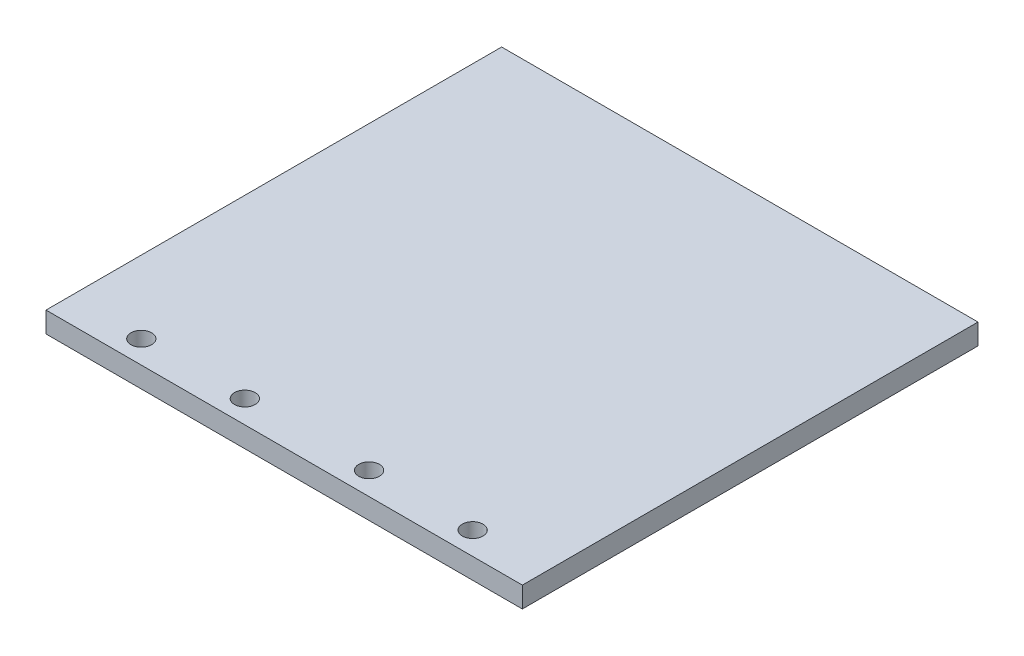
SolidWorks part; units mm, degrees
ref_plane "Front Plane" through (0, 0, 0) normal (0, 0, 1) x (1, 0, 0)
ref_plane "Top Plane" through (0, 0, 0) normal (0, 1, 0) x (1, 0, 0)
ref_plane "Right Plane" through (0, 0, 0) normal (1, 0, 0) x (0, 0, -1)
sketch "Sketch2" plane through (0, 0, 0) normal (0, 1, 0) x (1, 0, 0)
  line L0 (0, 92.2649) -> (0, -97.3417) construction
  line L1 (-57.5, 55) -> (57.5, 55)
  line L2 (-57.5, 55) -> (-57.5, -55)
  line L3 (-57.5, -55) -> (57.5, -55)
  line L4 (57.5, 55) -> (57.5, -55)
  line L5 (-77.6967, 0) -> (99.3282, 0) construction
  dimension "D1" = 115
  dimension "D2" = 110
extrude "Boss-Extrude1" add sketch "Sketch2" along normal blind 5
sketch "Sketch3" plane through (0, 0, 0) normal (0, -1, 0) x (1, 0, 0)
  line L0 (-63.5633, 49.5) -> (69.5866, 49.5) construction
  line L2 (-57.5, 55) -> (57.5, 55) construction
  line L3 (0, 53.104) -> (0, -54.2302) construction
  circle A2 centre (-40, 49.5) radius 2.5
  circle A3 centre (-15, 49.5) radius 2.5
  circle A4 centre (40, 49.5) radius 2.5
  circle A5 centre (15, 49.5) radius 2.5
  dimension "D1" = 5
  dimension "D2" = 5
  dimension "D3" = 25
  dimension "D4" = 3
  dimension "D5" = 15
extrude "Cut-Extrude1" cut sketch "Sketch3" against normal up to next
